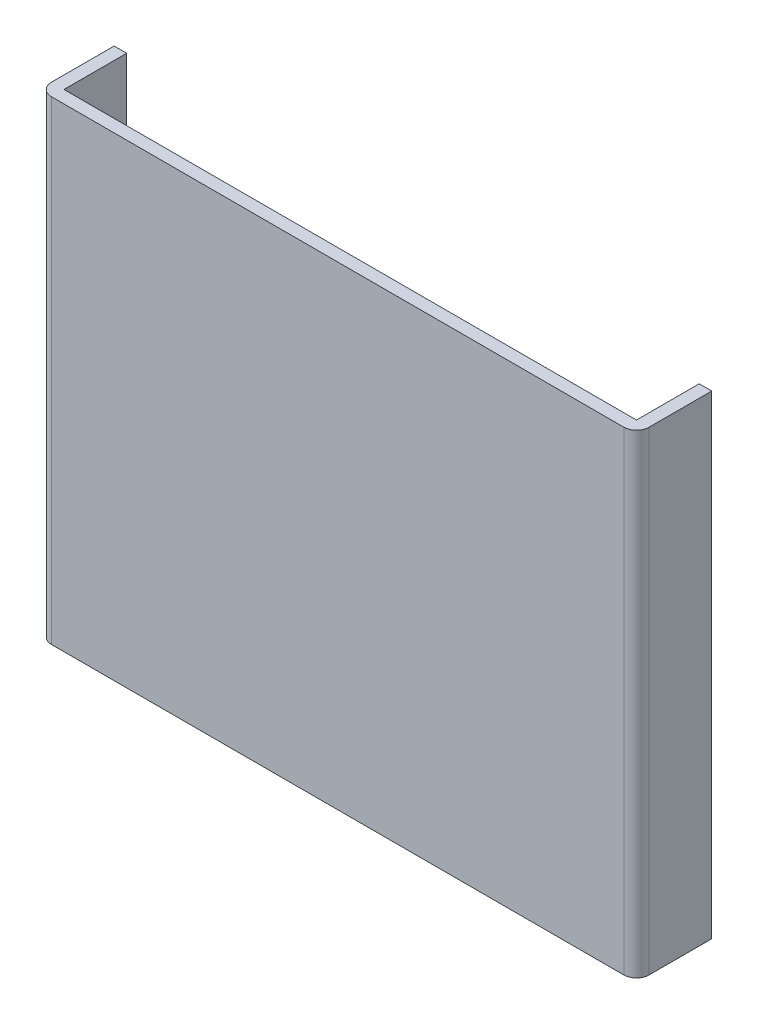
SolidWorks part; units mm, degrees
ref_plane "Front Plane" through (0, 0, 0) normal (0, 0, 1) x (1, 0, 0)
ref_plane "Top Plane" through (0, 0, 0) normal (0, 1, 0) x (1, 0, 0)
ref_plane "Right Plane" through (0, 0, 0) normal (1, 0, 0) x (0, 0, -1)
sketch "Sketch1" plane through (0, 0, 0) normal (0, 1, 0) x (1, 0, 0)
  line L0 (-18.6011, -3.5635) -> (-18.6011, -15.5635)
  line L5 (-18.6011, -15.5635) -> (76.6589, -15.5635)
  line L6 (76.6589, -15.5635) -> (76.6589, -3.5635)
  line L11 (76.6589, -3.5635) -> (74.6589, -3.5635)
  line L12 (74.6589, -3.5635) -> (74.6589, -13.5635)
  line L13 (74.6589, -13.5635) -> (-16.6011, -13.5635)
  line L14 (-16.6011, -13.5635) -> (-16.6011, -3.5635)
  line L15 (-16.6011, -3.5635) -> (-18.6011, -3.5635)
  line L16 (-16.6011, -13.5635) -> (-18.6011, -13.5635) construction
  line L17 (-16.6011, -13.5635) -> (-16.6011, -15.5635) construction
  line L18 (74.6589, -13.5635) -> (76.6589, -13.5635) construction
  dimension "D1" = 2
  dimension "D2" = 10
  dimension "D3" = 10
  dimension "D4" = 91.26
extrude "Boss-Extrude1" add sketch "Sketch1" along normal blind 75.62
fillet "Fillet1" radius 2 2 edges at (76.6589, 37.81, 15.5635) (-18.6011, 37.81, 15.5635)
